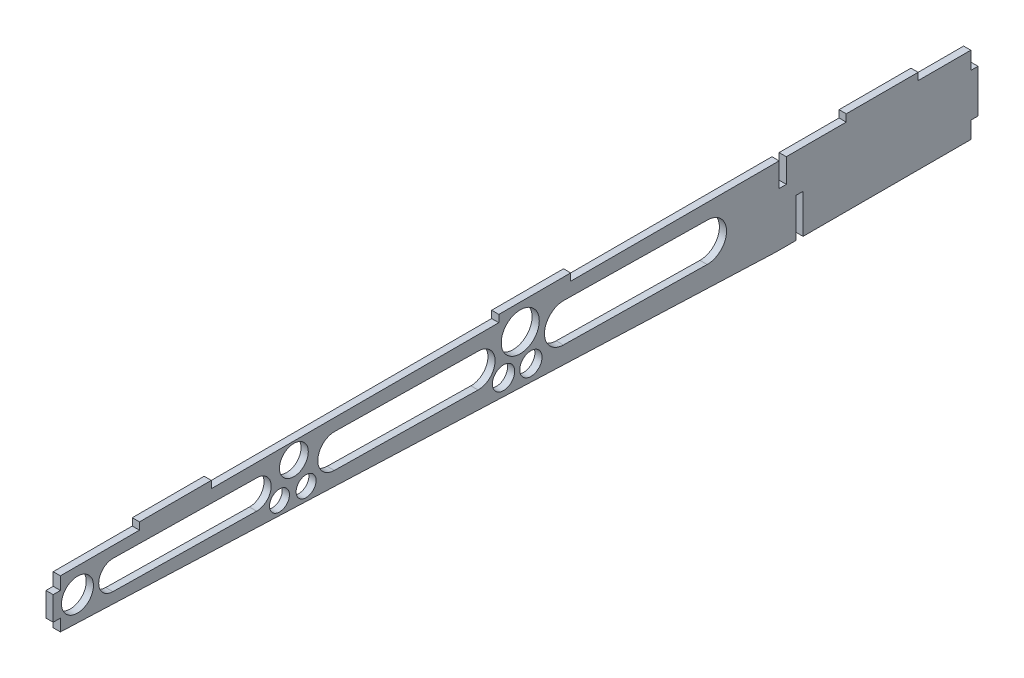
SolidWorks part; units mm, degrees
ref_plane "Front Plane" through (0, 0, 0) normal (0, 0, 1) x (1, 0, 0)
ref_plane "Top Plane" through (0, 0, 0) normal (0, 1, 0) x (1, 0, 0)
ref_plane "Right Plane" through (0, 0, 0) normal (1, 0, 0) x (0, 0, -1)
sketch "Sketch1" plane through (0, 0, 0) normal (1, 0, 0) x (0, 0, -1)
  line L0 (-383, 12.0163) -> (-84.3, 0)
  line L1 (-84.3, 0) -> (0, 0)
  line L2 (0, 0) -> (0, 32.31)
  line L3 (0, 32.31) -> (-383, 32.31)
  line L4 (-390.3, 32.31) -> (-390.3, 12.31) construction
  line L5 (-383, 32.31) -> (-383, 12.0163)
  line L6 (0, 55) -> (0, -55) construction
  line L7 (-390.3, 12.31) -> (-383, 12.0163) construction
  line L8 (-383, 32.31) -> (-390.3, 32.31) construction
  dimension "D1" = 20
  dimension "D2" = 32.31
  dimension "D3" = 84.3
  dimension "D4" = 177.696
  dimension "D5" = 390.3
  dimension "D6" = 383
extrude "Boss-Extrude1" add sketch "Sketch1" along normal blind 3
sketch "Sketch2" plane through (3, 0, 0) normal (1, 0, 0) x (0, 0, -1)
  line L0 (-383, 32.31) -> (-383, 12.0163) construction
  line L1 (-383, 27.0163) -> (-386, 27.0163)
  line L2 (-383, 27.0163) -> (-383, 17.0163)
  line L3 (-383, 17.0163) -> (-386, 17.0163)
  line L4 (-386, 27.0163) -> (-386, 17.0163)
  line L5 (0, 32.31) -> (-383, 32.31) construction
  line L6 (-350, 32.31) -> (-320, 32.31)
  line L7 (-350, 32.31) -> (-350, 35.31)
  line L8 (-350, 35.31) -> (-320, 35.31)
  line L9 (-320, 32.31) -> (-320, 35.31)
  line L10 (0, 1.65) -> (0, -1.65) construction
  line L11 (-55, 32.31) -> (-25, 32.31)
  line L12 (-55, 32.31) -> (-55, 35.31)
  line L13 (-55, 35.31) -> (-25, 35.31)
  line L14 (-25, 32.31) -> (-25, 35.31)
  line L16 (-200, 32.31) -> (-170, 32.31)
  line L17 (-200, 32.31) -> (-200, 35.31)
  line L18 (-200, 35.31) -> (-170, 35.31)
  line L19 (-170, 32.31) -> (-170, 35.31)
  dimension "D1" = 10
  dimension "D2" = 5
  dimension "D3" = 3
  dimension "D4" = 3
  dimension "D5" = 30
  dimension "D6" = 25
  dimension "D7" = 30
  dimension "D8" = 320
  dimension "D9" = 170
  dimension "D10" = 85.7
  dimension "D11" = 235.7
extrude "Boss-Extrude2" add sketch "Sketch2" against normal up to surface (3 mm away) up to face at (0, 15.3273, 170.06)
sketch "Sketch3" plane through (3, 0, 0) normal (1, 0, 0) x (0, 0, -1)
  line L0 (-386, 22.0163) -> (0, 16.155) construction
  line L1 (-386, 27.0163) -> (-386, 17.0163) construction
  line L2 (0, 0) -> (0, 32.31) construction
  line L3 (-361, 21.6367) -> (-301, 20.7256) construction
  line L4 (-360.9089, 27.636) -> (-300.9089, 26.7249)
  line L5 (-361.0911, 15.6374) -> (-301.0911, 14.7263)
  line L6 (-268.5536, 20.2329) -> (-208.5536, 19.3218) construction
  line L7 (-268.4473, 27.2321) -> (-208.4473, 26.321)
  line L8 (-268.6599, 13.2337) -> (-208.6599, 12.3226)
  line L9 (-172.9385, 18.781) -> (-112.9385, 17.8699) construction
  line L10 (-172.817, 26.7801) -> (-112.817, 25.869)
  line L11 (-173.06, 10.782) -> (-113.06, 9.8709)
  arc A0 (-360.9089, 27.636) -> (-361.0911, 15.6374) centre (-361, 21.6367) ccw
  arc A1 (-301.0911, 14.7263) -> (-300.9089, 26.7249) centre (-301, 20.7256) ccw
  arc A2 (-268.4473, 27.2321) -> (-268.6599, 13.2337) centre (-268.5536, 20.2329) ccw
  arc A3 (-208.6599, 12.3226) -> (-208.4473, 26.321) centre (-208.5536, 19.3218) ccw
  arc A4 (-172.817, 26.7801) -> (-173.06, 10.782) centre (-172.9385, 18.781) ccw
  arc A5 (-113.06, 9.8709) -> (-112.817, 25.869) centre (-112.9385, 17.8699) ccw
  point P8 (-331, 21.1812)
  point P13 (-238.5536, 19.7774)
  point P20 (-142.9385, 18.3255)
  dimension "D1" = 6
  dimension "D5" = 7
  dimension "D7" = 8
  dimension "D2" = 60
  dimension "D3" = 25
  dimension "D4" = 60
  dimension "D6" = 60
extrude "Cut-Extrude1" cut sketch "Sketch3" against normal blind 10
sketch "Sketch4" plane through (3, 0, 0) normal (1, 0, 0) x (0, 0, -1)
  line L0 (-55, 32.31) -> (-170, 32.31) construction
  line L1 (-80, 32.31) -> (-83, 32.31)
  line L2 (-80, 32.31) -> (-80, 22.31)
  line L3 (-80, 22.31) -> (-83, 22.31)
  line L4 (-83, 32.31) -> (-83, 22.31)
  line L5 (0, 0) -> (0, 32.31) construction
  line L6 (-84.3, 0) -> (0, 0) construction
  line L7 (-76, 0) -> (-73, 0)
  line L8 (-76, 0) -> (-76, 16.31)
  line L9 (-76, 16.31) -> (-73, 16.31)
  line L10 (-73, 0) -> (-73, 16.31)
  dimension "D1" = 3
  dimension "D2" = 83
  dimension "D3" = 10
  dimension "D4" = 3
  dimension "D5" = 16.31
  dimension "D6" = 73
extrude "Cut-Extrude2" cut sketch "Sketch4" against normal blind 10
sketch "Sketch5" plane through (3, 0, 0) normal (1, 0, 0) x (0, 0, -1)
  line L0 (0, 0) -> (0, 32.31) construction
  line L1 (0, 25) -> (-3, 25)
  line L2 (0, 25) -> (0, 38.7035)
  line L3 (0, 38.7035) -> (-3, 38.7035)
  line L4 (-3, 25) -> (-3, 38.7035)
  line L6 (0, 7) -> (-3, 7)
  line L7 (0, 7) -> (0, -6.7914)
  line L8 (0, -6.7914) -> (-3, -6.7914)
  line L9 (-3, 7) -> (-3, -6.7914)
  line L10 (-84.3, 0) -> (-76, 0) construction
  dimension "D1" = 3
  dimension "D2" = 18
  dimension "D3" = 7
  dimension "D4" = 3
extrude "Cut-Extrude3" cut sketch "Sketch5" against normal blind 10
sketch "Sketch6" plane through (3, 0, 0) normal (1, 0, 0) x (0, 0, -1)
  circle A0 centre (-375.8654, 21.9285) radius 6.6659
  circle A1 centre (-285.5441, 25.4353) radius 6.0147
  circle A2 centre (-280.4436, 13.4491) radius 4.1675
  circle A3 centre (-291.5589, 13.8316) radius 4.1675
  circle A4 centre (-191.0576, 24.5427) radius 7.9427
  circle A5 centre (-186.6146, 10.8424) radius 4.6589
  circle A6 centre (-198.0379, 11.4471) radius 4.6589
extrude "Cut-Extrude4" cut sketch "Sketch6" against normal blind 10
